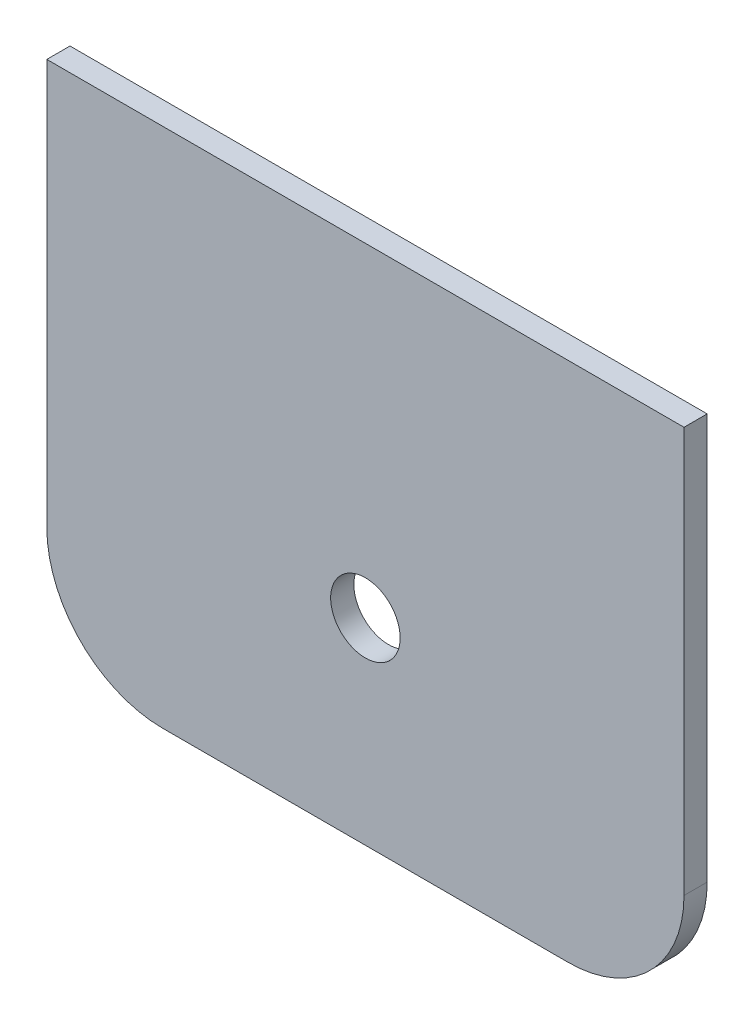
SolidWorks part; units mm, degrees
material "Stal węglowa"
ref_plane "Płaszczyzna XY" through (0, 0, 0) normal (0, 0, 1) x (1, 0, 0)
ref_plane "Płaszczyzna XZ" through (0, 0, 0) normal (0, 1, 0) x (1, 0, 0)
ref_plane "Płaszczyzna YZ" through (0, 0, 0) normal (1, 0, 0) x (0, 0, -1)
sketch "Szkic1" plane through (0, 0, 0) normal (0, 0, 1) x (1, 0, 0)
  line L0 (27.5, 699.4225) -> (-27.5, 699.4225)
  line L1 (-27.5, 699.4225) -> (-27.5, 744.4225)
  line L2 (-27.5, 744.4225) -> (27.5, 744.4225)
  line L3 (27.5, 744.4225) -> (27.5, 699.4225)
extrude "Dodanie-wyciągnięcie1" add sketch "Szkic1" along normal blind 2
fillet "Zaokrąglenie1" radius 10 1 edges at (-27.5, 699.4225, 1)
fillet "Zaokrąglenie2" radius 10 1 edges at (27.5, 699.4225, 1)
sketch "Szkic2" plane through (0, 0, 2) normal (0, 0, 1) x (1, 0, 0)
  line L0 (-27.5, 699.4225) -> (-27.5, 744.4225) construction
  line L2 (27.5, 699.4225) -> (-27.5, 699.4225) construction
  circle A0 centre (0, 716.4225) radius 3
  dimension "D1" = 27.5
  dimension "D2" = 17
extrude "Wytnij-wyciągnięcie2" cut sketch "Szkic2" against normal blind 2
